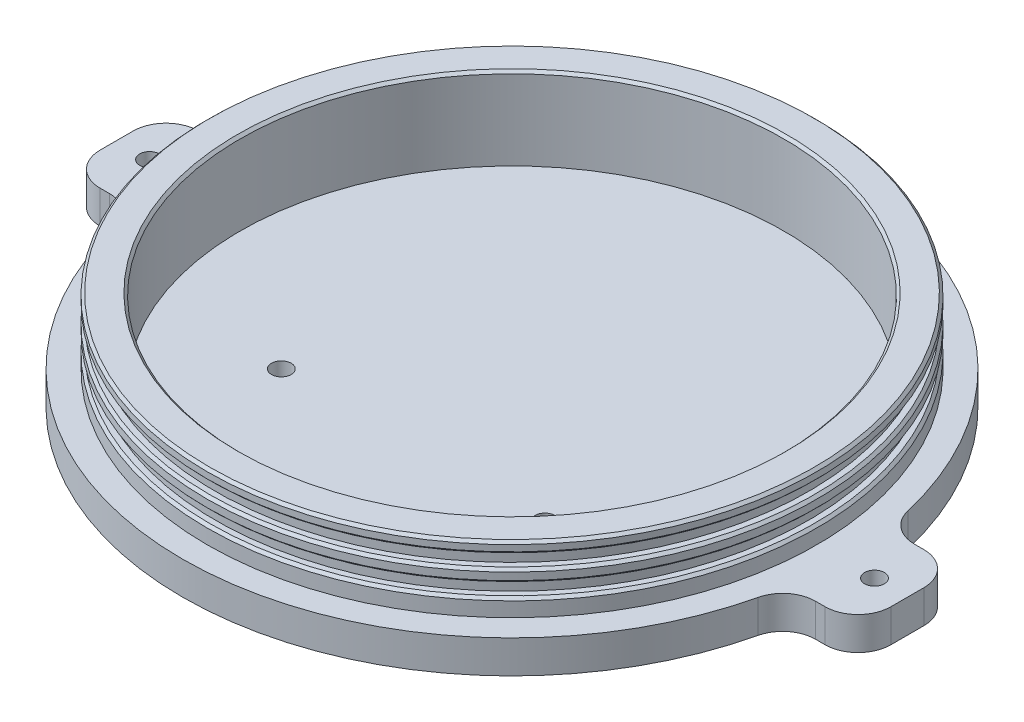
SolidWorks part; units mm, degrees
material "6061 Alloy"
ref_plane "Front Plane" through (0, 0, 0) normal (0, 0, 1) x (1, 0, 0)
ref_plane "Top Plane" through (0, 0, 0) normal (0, 1, 0) x (1, 0, 0)
ref_plane "Right Plane" through (0, 0, 0) normal (1, 0, 0) x (0, 0, -1)
sketch "Sketch1" plane through (0, 0, 0) normal (0, 1, 0) x (1, 0, 0)
  circle A0 centre (0, 0) radius 63.5
extrude "Extrude1" add sketch "Sketch1" along normal blind 6.35
sketch "Sketch2" plane through (0, 6.35, 0) normal (0, 1, 0) x (-1, 0, 0)
  circle A0 centre (0, 0) radius 58.7375
  circle A1 centre (0, 0) radius 52.3875
extrude "Extrude2" add sketch "Sketch2" along normal blind 12.7
sketch "Sketch3" plane through (0, 0, 0) normal (1, 0, 0) x (0, 0, -1)
  line L0 (-58.7375, 19.05) -> (-58.7375, 6.35) construction
  line L1 (-58.7375, 16.8472) -> (-57.15, 16.8472)
  line L2 (-58.7375, 16.8472) -> (-58.7375, 14.4659)
  line L3 (-58.7375, 14.4659) -> (-57.15, 14.4659)
  line L4 (-57.15, 16.8472) -> (-57.15, 14.4659)
  line L5 (0, 0) -> (0, 23.3452) construction
  line L6 (-58.7375, 12.033) -> (-57.15, 12.033)
  line L7 (-58.7375, 12.033) -> (-58.7375, 9.6518)
  line L8 (-58.7375, 9.6518) -> (-57.15, 9.6518)
  line L9 (-57.15, 12.033) -> (-57.15, 9.6518)
  dimension "D1" = 1.5875
  dimension "D2" = 2.3812
revolve "Cut-Revolve1" cut sketch "Sketch3" angle 360 about L5
chamfer "Chamfer1" distance 0.5 angle 45 6 edges at (0, 9.6518, -58.7375) (0, 12.033, -58.7375) (0, 14.4659, -58.7375) (0, 16.8472, -58.7375) (0, 19.05, 58.7375) (0, 19.05, 52.3875)
sketch "Sketch5" plane through (0, 0, 0) normal (0, -1, 0) x (1, 0, 0)
  line L1 (-69.85, 9.525) -> (69.85, 9.525)
  line L2 (-76.2, 3.175) -> (-76.2, -3.175)
  line L3 (-69.85, -9.525) -> (69.85, -9.525)
  line L4 (76.2, 3.175) -> (76.2, -3.175)
  arc A0 (-69.85, 9.525) -> (-76.2, 3.175) centre (-69.85, 3.175) ccw
  arc A1 (-69.85, -9.525) -> (-76.2, -3.175) centre (-69.85, -3.175) cw
  arc A2 (76.2, -3.175) -> (69.85, -9.525) centre (69.85, -3.175) cw
  arc A3 (76.2, 3.175) -> (69.85, 9.525) centre (69.85, 3.175) ccw
  point P7 (-76.2, 9.525)
  point P10 (-76.2, -9.525)
  point P15 (76.2, 9.525)
  dimension "D5" = 6.35
  dimension "D1" = 152.4
  dimension "D2" = 76.2
  dimension "D3" = 19.05
  dimension "D4" = 9.525
extrude "Extrude3" add sketch "Sketch5" against normal up to surface (6.35 mm away) up to face at (0, 6.35, 52.3875)
hole_wizard "#6 Clearance Hole1" positions "3DSketch1" profile "Sketch6" hole size "#6" standard "Ansi Inch"
sketch3d "3DSketch1"
  line L0 (-62.7816, 0, 9.525) -> (-69.85, 0, 9.525) construction
  line L1 (69.85, 0, 9.525) -> (62.7816, 0, 9.525) construction
  line L2 (-76.2, 0, 3.175) -> (-76.2, 0, -3.175) construction
  line L3 (76.2, 0, -3.175) -> (76.2, 0, 3.175) construction
  point P0 (-69.85, 0, 0)
  point P2 (69.85, 0, 0)
  dimension "D1" = 9.525
  dimension "D2" = 9.525
  dimension "D3" = 6.35
  dimension "D4" = 6.35
sketch "Sketch6" plane through (-69.85, 0, 0) normal (1, 0, 0) x (0, 0, -1)
  line L0 (0, 0) -> (0, 331.3408)
  line L1 (0, 331.3408) -> (1.8986, 330.2)
  line L2 (1.8986, 330.2) -> (1.8986, 0)
  line L5 (1.8986, 0) -> (0, 0)
  line L10 (0, 331.3408) -> (-1.8987, 330.2) construction
  line L11 (0, -6.35) -> (0, 107.95) construction
  dimension "Hole Dia." = 3.7973
  dimension "Hole Depth" = 330.2
  dimension "Drill Angle" = 118
fillet "Fillet1" radius 6.35 4 edges at (62.7816, 3.175, -9.525) (-62.7816, 3.175, -9.525) (-62.7816, 3.175, 9.525) (62.7816, 3.175, 9.525)
hole_wizard "#6 Clearance Hole2" positions "3DSketch2" profile "Sketch7" hole size "#6" standard "Ansi Inch"
sketch3d "3DSketch2"
  line L0 (0, 0, 0) -> (0, 0, 38.4573) construction
  line L2 (0, 0, 0) -> (31.4926, 0, 0) construction
  point P0 (25.4, 0, 19.05)
  point P2 (25.4, 0, 38.1)
  point P4 (-25.4, 0, 38.1)
  point P6 (-25.4, 0, 19.05)
  dimension "D1" = 19.05
  dimension "D2" = 50.8
  dimension "D3" = 25.4
  dimension "D4" = 19.05
sketch "Sketch7" plane through (25.4, 0, 19.05) normal (1, 0, 0) x (0, 0, -1)
  line L0 (0, 0) -> (0, 26.5408)
  line L1 (0, 26.5408) -> (1.8986, 25.4)
  line L2 (1.8986, 25.4) -> (1.8986, 0)
  line L5 (1.8986, 0) -> (0, 0)
  line L10 (0, 26.5408) -> (-1.8987, 25.4) construction
  line L11 (0, -6.35) -> (0, 107.95) construction
  dimension "Hole Dia." = 3.7973
  dimension "Hole Depth" = 25.4
  dimension "Drill Angle" = 118
sketch "Sketch8" plane through (0, 6.35, 0) normal (0, 1, 0) x (-1, 0, 0)
  circle A0 centre (0, 0) radius 52.3875
extrude "Cut-Extrude1" cut sketch "Sketch8" against normal blind 3.175
